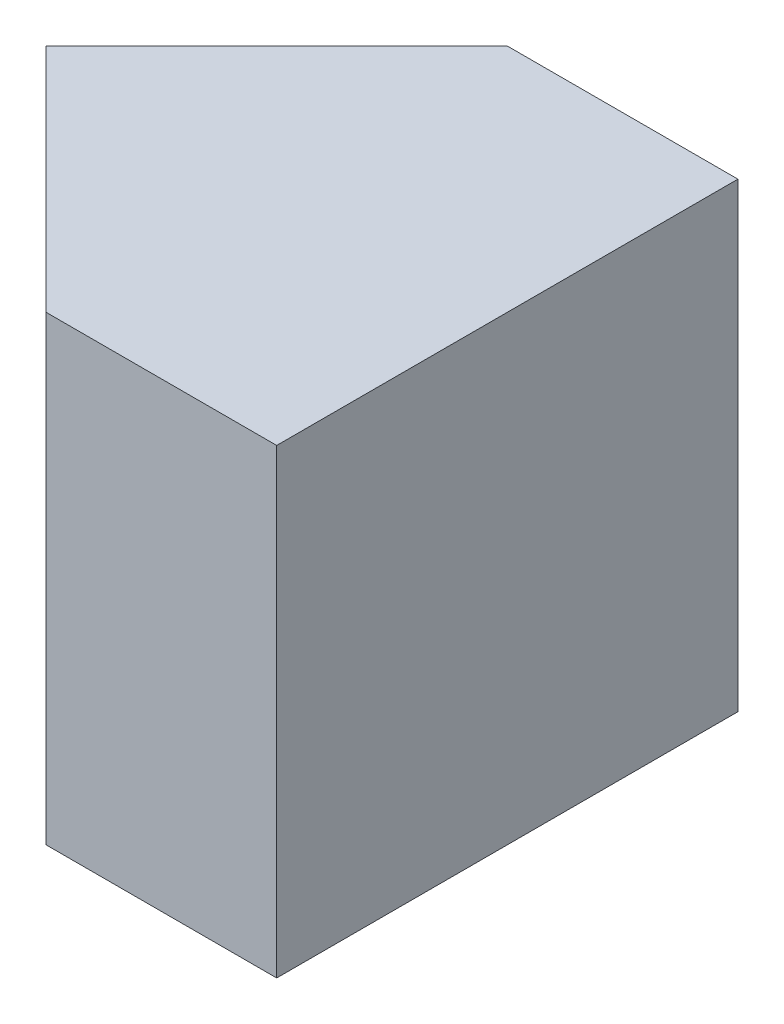
SolidWorks part; units mm, degrees
ref_plane "Front Plane" through (0, 0, 0) normal (0, 0, 1) x (1, 0, 0)
ref_plane "Top Plane" through (0, 0, 0) normal (0, 1, 0) x (1, 0, 0)
ref_plane "Right Plane" through (0, 0, 0) normal (1, 0, 0) x (0, 0, -1)
sketch "Sketch1" plane through (0, 0, 0) normal (0, 0, 1) x (1, 0, 0)
  line L1 (0, 0) -> (20, 0)
  line L2 (0, 0) -> (0, 20)
  line L3 (0, 20) -> (20, 20)
  line L4 (20, 0) -> (20, 20)
  dimension "D1" = 20
  dimension "D2" = 20
extrude "Boss-Extrude1" add sketch "Sketch1" along normal blind 20
sketch "Sketch2" plane through (0, 20, 0) normal (0, 1, 0) x (1, 0, 0)
  line L0 (0, 0) -> (10, 0)
  line L1 (20, 0) -> (0, 0) construction
  line L2 (10, 0) -> (0, -10)
  line L3 (0, -20) -> (0, 0) construction
  line L4 (0, -10) -> (0, 0)
extrude "Cut-Extrude1" cut sketch "Sketch2" against normal blind 20
sketch "Sketch3" plane through (0, 20, 0) normal (0, 1, 0) x (1, 0, 0)
  line L0 (0, -10) -> (0, -20)
  line L1 (0, -20) -> (10, -20)
  line L2 (20, -20) -> (0, -20) construction
  line L3 (10, -20) -> (0, -10)
extrude "Cut-Extrude2" cut sketch "Sketch3" against normal blind 20
